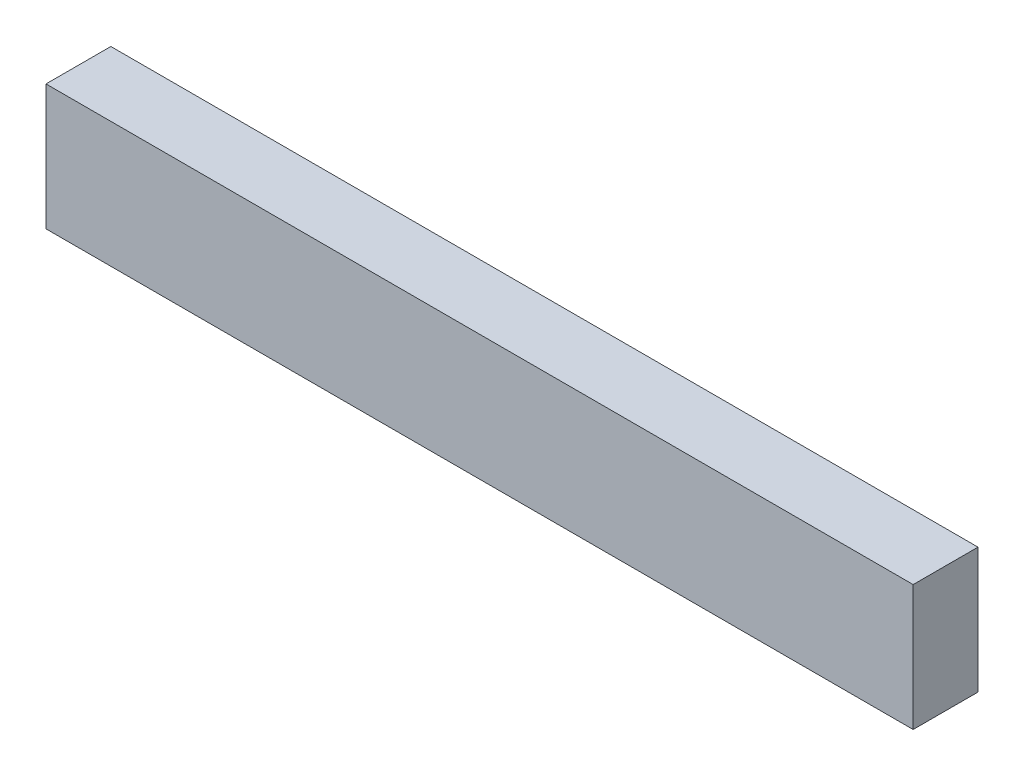
SolidWorks part; units mm, degrees
material "Silicon Rubber"
ref_plane "Front" through (0, 0, 0) normal (0, 0, 1) x (1, 0, 0)
ref_plane "Top" through (0, 0, 0) normal (0, 1, 0) x (1, 0, 0)
ref_plane "Right" through (0, 0, 0) normal (1, 0, 0) x (0, 0, -1)
sketch "Sketch1" plane through (0, 0, 0) normal (0, 0, 1) x (1, 0, 0)
  line L0 (22.5, 243.493) -> (22.5, 256.193) construction
  line L1 (-21.23, 246.2362) -> (21.23, 246.2362)
  line L2 (-21.23, 246.2362) -> (-21.23, 252.383)
  line L3 (-21.23, 252.383) -> (21.23, 252.383)
  line L4 (21.23, 246.2362) -> (21.23, 252.383)
  line L6 (25.4954, 246.2362) -> (-25.4954, 246.2362) construction
  line L7 (-22.5, 256.193) -> (-22.5, 243.493) construction
  line L8 (-25.4954, 256.193) -> (25.4954, 256.193) construction
  point P0 (0, 0)
  dimension "D1" = 1.27
  dimension "D2" = 1.27
  dimension "D3" = 3.81
extrude "Boss-Extrude1" add sketch "Sketch1" along normal blind 3.175
